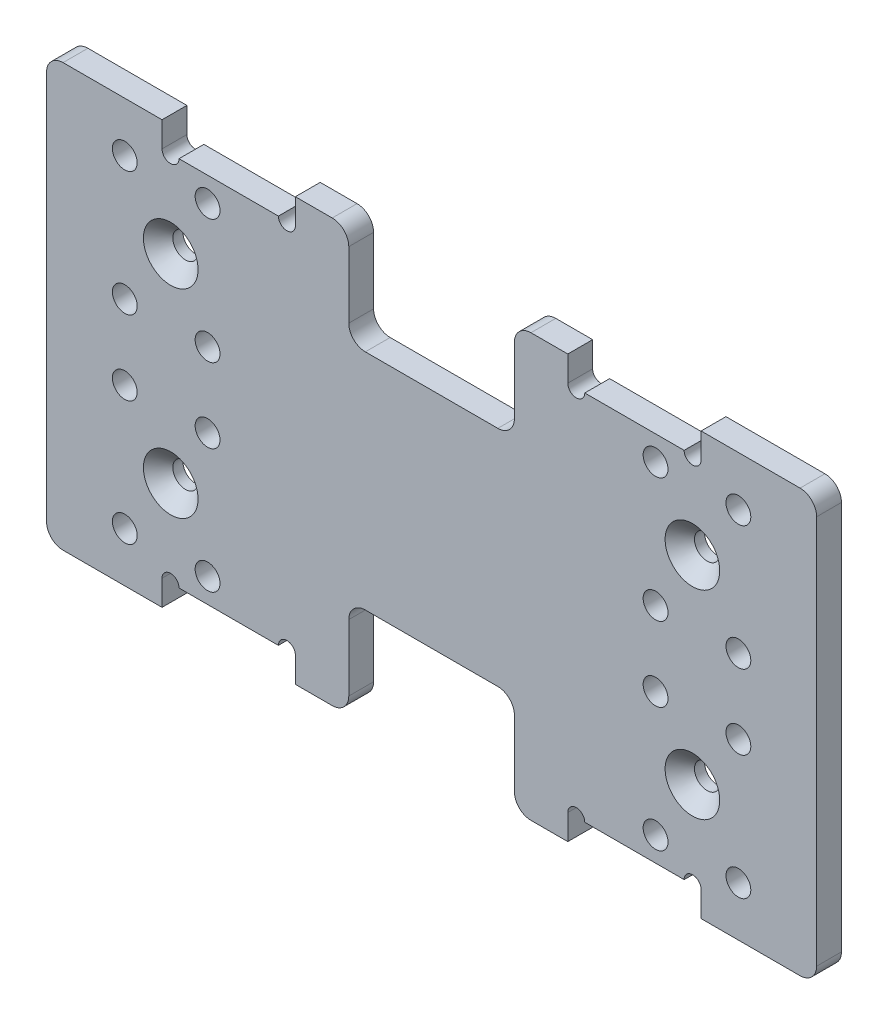
SolidWorks part; units mm, degrees
material "Thornel Mat VMA"
ref_plane "前视基准面" through (0, 0, 0) normal (0, 0, 1) x (1, 0, 0)
ref_plane "上视基准面" through (0, 0, 0) normal (0, 1, 0) x (1, 0, 0)
ref_plane "右视基准面" through (0, 0, 0) normal (1, 0, 0) x (0, 0, -1)
sketch "草图1" plane through (0, 0, 0) normal (0, 0, 1) x (1, 0, 0)
  line L1 (-46.5, -25.5) -> (46.5, -25.5)
  line L2 (-46.5, -25.5) -> (-46.5, 25.5)
  line L3 (-46.5, 25.5) -> (46.5, 25.5)
  line L4 (46.5, -25.5) -> (46.5, 25.5)
  line L5 (0, 25.5) -> (0, -25.5) construction
  line L6 (-46.5, 0) -> (46.5, 0) construction
  point P0 (0, 0)
  dimension "D1" = 93
  dimension "D2" = 51
extrude "凸台-拉伸1" add sketch "草图1" along normal mid plane 3
sketch "草图2" plane through (0, 0, 1.5) normal (0, 0, 1) x (1, 0, 0)
  line L0 (-31.5, 12) -> (31.5, 12) construction
  line L1 (46.5, -25.5) -> (46.5, 25.5) construction
  line L2 (0, 0) -> (0, 12) construction
  line L3 (46.5, 25.5) -> (-46.5, 25.5) construction
  circle A0 centre (-31.5, 12) radius 1.525
  circle A1 centre (31.5, 12) radius 1.525
  point P4 (0, 12)
  dimension "D2" = 3.05
  dimension "D1" = 15
  dimension "D3" = 13.5
extrude "切除-拉伸1" cut sketch "草图2" against normal mid plane 10
hole_wizard "M3 十字槽半沉头木螺钉的锥形沉头孔1" positions "草图3" profile "草图4" countersink size "M3" standard "GB"
sketch "草图3" plane through (0, 0, 1.5) normal (0, 0, 1) x (1, 0, 0)
  point P0 (-31.5, 12)
  point P3 (31.5, 12)
sketch "草图4" plane through (-31.5, 12, 1.5) normal (1, 0, 0) x (0, -1, 0)
  line L0 (0, 0) -> (0, 12.4013)
  line L1 (0, 12.4013) -> (1.5, 11.5)
  line L2 (1.5, 11.5) -> (1.5, 1.8)
  line L3 (1.5, 1.8) -> (3.3, 0)
  line L5 (3.3, 0) -> (0, 0)
  line L6 (-1.5, 1.8) -> (-3.3, 0) construction
  line L10 (0, 12.4013) -> (-1.5, 11.5) construction
  line L11 (0, -6.35) -> (0, 107.95) construction
  dimension "孔直径" = 3
  dimension "孔深度" = 11.5
  dimension "近端锥形沉头孔直径" = 6.6
  dimension "近端锥形沉头孔角度" = 90
  dimension "导头角度" = 118
sketch "草图5" plane through (0, 0, -1.5) normal (0, 0, -1) x (-1, 0, 0)
  line L0 (0, 0) -> (0, 33.2629) construction
  line L1 (-37.05, 19.5) -> (-27.05, 19.5) construction
  line L2 (-37.05, 19.5) -> (-37.05, 4.5) construction
  line L3 (-37.05, 4.5) -> (-27.05, 4.5) construction
  line L4 (-27.05, 19.5) -> (-27.05, 4.5) construction
  line L5 (-32.05, 4.5) -> (-32.05, 19.5) construction
  line L6 (-37.05, 12) -> (-27.05, 12) construction
  line L7 (37.05, 12) -> (27.05, 12) construction
  line L8 (32.05, 4.5) -> (32.05, 19.5) construction
  line L9 (27.05, 19.5) -> (27.05, 4.5) construction
  line L10 (37.05, 4.5) -> (27.05, 4.5) construction
  line L11 (37.05, 19.5) -> (37.05, 4.5) construction
  line L12 (37.05, 19.5) -> (27.05, 19.5) construction
  circle A0 centre (-27.05, 4.5) radius 1.5 construction
  circle A1 centre (-37.05, 4.5) radius 1.5 construction
  circle A2 centre (-37.05, 19.5) radius 1.5 construction
  circle A3 centre (-27.05, 4.5) radius 1.5
  circle A4 centre (-37.05, 4.5) radius 1.5
  circle A5 centre (-37.05, 19.5) radius 1.5
  circle A6 centre (-27.05, 19.5) radius 1.5
  circle A7 centre (27.05, 19.5) radius 1.5
  circle A8 centre (37.05, 19.5) radius 1.5
  circle A9 centre (37.05, 4.5) radius 1.5
  circle A10 centre (27.05, 4.5) radius 1.5
  point P9 (-32.05, 12)
  point P25 (32.05, 12)
extrude "切除-拉伸2" cut sketch "草图5" against normal mid plane 10
mirror "镜向1" about plane through (0, 0, 0) normal (0, 1, 0) of "切除-拉伸2"
mirror "镜向2" about plane through (0, 0, 0) normal (0, 1, 0) of "M3 十字槽半沉头木螺钉的锥形沉头孔1", "切除-拉伸1"
sketch "草图7" plane through (0, 0, -1.5) normal (0, 0, -1) x (-1, 0, 0)
  line L0 (46.5, -25.5) -> (-46.5, -25.5) construction
  line L1 (-10, -37.5) -> (10, -37.5)
  line L2 (-10, -37.5) -> (-10, -13.5)
  line L3 (-10, -13.5) -> (10, -13.5)
  line L4 (10, -37.5) -> (10, -13.5)
  line L5 (0, -13.5) -> (0, -37.5) construction
  line L6 (-10, -25.5) -> (10, -25.5) construction
  point P0 (0, -25.5)
  dimension "D1" = 12
  dimension "D2" = 20
extrude "切除-拉伸3" cut sketch "草图7" against normal blind 10
mirror "镜向3" about plane through (0, 0, 0) normal (0, 1, 0) of "切除-拉伸3"
fillet "圆角1" radius 2 12 edges at (-10, 13.5, 0) (10, 13.5, 0) (10, 25.5, 0) (46.5, 25.5, 0) (46.5, -25.5, 0) (-10, -13.5, 0) (-10, -25.5, 0) (-46.5, -25.5, 0) (-46.5, 25.5, 0) (-10, 25.5, 0) (10, -13.5, 0) (10, -25.5, 0)
sketch "草图8" plane through (0, 0, -1.5) normal (0, 0, -1) x (-1, 0, 0)
  line L0 (-32.55, 25.55) -> (-32.55, 22.45)
  line L1 (-32.55, 22.45) -> (-16.45, 22.45)
  line L2 (-16.45, 22.45) -> (-16.45, 25.55)
  line L3 (-16.45, 25.55) -> (-32.55, 25.55)
  line L4 (-32.5, 25.5) -> (-32.5, 22.5)
  line L5 (-32.5, 22.5) -> (-16.5, 22.5)
  line L6 (-16.5, 22.5) -> (-16.5, 25.5)
  line L7 (-16.5, 25.5) -> (-32.5, 25.5)
  line L8 (-32.5, 25.5) -> (-32.5, 22.5) construction
  line L9 (-32.5, 22.5) -> (-16.5, 22.5) construction
  line L10 (-16.5, 22.5) -> (-16.5, 25.5) construction
  line L11 (-16.5, 25.5) -> (-32.5, 25.5) construction
  dimension "D1" = 0
  dimension "D2" = 0.05
extrude "切除-拉伸4" cut sketch "草图8" against normal up to surface (3 mm away) up to face at (34.8, 12, 1.5)
mirror "镜向4" about plane through (0, 0, 0) normal (1, 0, 0) of "切除-拉伸4"
mirror "镜向5" about plane through (0, 0, 0) normal (0, 1, 0) of "镜向4", "切除-拉伸4"
sketch "草图9" plane through (0, 0, 1.5) normal (0, 0, 1) x (1, 0, 0)
  line L0 (-16.45, 22.45) -> (-32.55, 22.45) construction
  line L1 (0, 0) -> (0, 30.847) construction
  circle A0 centre (-31.525, 22.45) radius 1.025
  circle A1 centre (-17.475, 22.45) radius 1.025
  circle A2 centre (17.475, 22.45) radius 1.025
  circle A3 centre (31.525, 22.45) radius 1.025
  dimension "D1" = 2.05
extrude "切除-拉伸5" cut sketch "草图9" against normal up to surface (3 mm away) up to face at (-33.025, -12, -1.5)
mirror "镜向6" about plane through (0, 0, 0) normal (0, 1, 0) of "切除-拉伸5"
